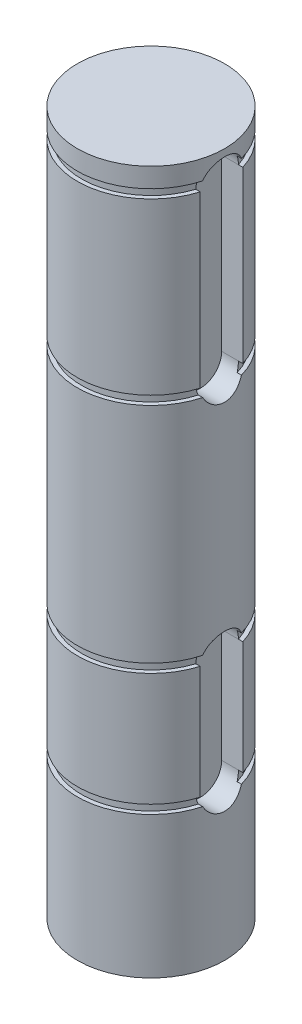
SolidWorks part; units mm, degrees
ref_plane "Front Plane" through (0, 0, 0) normal (0, 0, 1) x (1, 0, 0)
ref_plane "Top Plane" through (0, 0, 0) normal (0, 1, 0) x (1, 0, 0)
ref_plane "Right Plane" through (0, 0, 0) normal (1, 0, 0) x (0, 0, -1)
sketch "Sketch1" plane through (0, 0, 0) normal (0, 1, 0) x (1, 0, 0)
  circle A0 centre (0, 0) radius 8.255
extrude "Boss-Extrude1" add sketch "Sketch1" along normal blind 78.7908 contours A0
sketch "Sketch3" plane through (0, 0, 0) normal (1, 0, 0) x (0, 0, -1)
  line L0 (-8.255, 0) -> (8.255, 0) construction
  line L1 (-35.9296, 16.8656) -> (-7.7851, 16.8656)
  line L2 (-35.9296, 16.8656) -> (-35.9296, 15.875)
  line L3 (-35.9296, 15.875) -> (-7.7851, 15.875)
  line L4 (-7.7851, 16.8656) -> (-7.7851, 15.875)
  line L5 (-8.255, 78.7908) -> (-8.255, 0) construction
  line L6 (0, 29.9273) -> (0, 6.5085) construction
  dimension "D1" = 28.1445
  dimension "D2" = 15.875
  dimension "D3" = 0.9906
  dimension "D4" = 0.4699
revolve "Cut-Revolve1" cut sketch "Sketch3" angle 360 about L6
sketch "Sketch4" plane through (0, 0, 0) normal (1, 0, 0) x (0, 0, -1)
  line L0 (-7.7851, 16.8656) -> (7.7851, 16.8656) construction
  line L1 (-20.6586, 30.5562) -> (-7.7851, 30.5562)
  line L2 (-20.6586, 30.5562) -> (-20.6586, 29.5656)
  line L3 (-20.6586, 29.5656) -> (-7.7851, 29.5656)
  line L4 (-7.7851, 30.5562) -> (-7.7851, 29.5656)
  line L5 (-8.255, 78.7908) -> (-8.255, 16.8656) construction
  line L6 (0, 33.7907) -> (0, 24.3351) construction
  dimension "D1" = 12.7
  dimension "D2" = 0.9906
  dimension "D3" = 0.4699
revolve "Cut-Revolve2" cut sketch "Sketch4" angle 360 about L6
sketch "Sketch5" plane through (0, 0, 0) normal (1, 0, 0) x (0, 0, -1)
  line L0 (-7.7851, 30.5562) -> (7.7851, 30.5562) construction
  line L1 (-26.2954, 56.5658) -> (-7.7851, 56.5658)
  line L2 (-26.2954, 56.5658) -> (-26.2954, 55.5752)
  line L3 (-26.2954, 55.5752) -> (-7.7851, 55.5752)
  line L4 (-7.7851, 56.5658) -> (-7.7851, 55.5752)
  line L5 (-8.255, 78.7908) -> (-8.255, 30.5562) construction
  line L6 (0, 60.6078) -> (0, 49.3632) construction
  dimension "D1" = 25.019
  dimension "D2" = 0.9906
  dimension "D3" = 0.4699
revolve "Cut-Revolve3" cut sketch "Sketch5" angle 360 about L6
sketch "Sketch6" plane through (0, 0, 0) normal (1, 0, 0) x (0, 0, -1)
  line L0 (-7.7851, 56.5658) -> (7.7851, 56.5658) construction
  line L1 (-21.1239, 76.6064) -> (-7.7851, 76.6064)
  line L2 (-21.1239, 76.6064) -> (-21.1239, 75.6158)
  line L3 (-21.1239, 75.6158) -> (-7.7851, 75.6158)
  line L4 (-7.7851, 76.6064) -> (-7.7851, 75.6158)
  line L5 (-8.255, 78.7908) -> (-8.255, 56.5658) construction
  line L6 (0, 77.1554) -> (0, 69.2288) construction
  dimension "D1" = 19.05
  dimension "D2" = 0.9906
  dimension "D3" = 0.4699
revolve "Cut-Revolve4" cut sketch "Sketch6" angle 360 about L6
ref_plane "Plane1" through (8.2804, 0, 0) normal (1, 0, 0) x (0, 0, -1)
sketch "Sketch7" plane through (8.2804, 0, 0) normal (1, 0, 0) x (0, 0, -1)
  line L0 (0, 75.6158) -> (0, 56.5658) construction
  line L1 (8.255, 75.6158) -> (-8.255, 75.6158) construction
  line L2 (-7.7851, 56.5658) -> (7.7851, 56.5658) construction
  line L3 (2.3876, 75.6158) -> (2.3876, 56.5658)
  line L4 (-2.3876, 75.6158) -> (-2.3876, 56.5658)
  arc A0 (2.3876, 75.6158) -> (-2.3876, 75.6158) centre (0, 75.6158) ccw
  arc A1 (-2.3876, 56.5658) -> (2.3876, 56.5658) centre (0, 56.5658) ccw
  point P6 (0, 66.0908)
extrude "Cut-Extrude2" cut sketch "Sketch7" against normal blind 2.7432 contours L4 A1 L3 A0
sketch "Sketch8" plane through (8.2804, 0, 0) normal (1, 0, 0) x (0, 0, -1)
  line L0 (0, 29.5656) -> (0, 16.8656) construction
  line L1 (8.255, 29.5656) -> (-8.255, 29.5656) construction
  line L2 (-7.7851, 16.8656) -> (7.7851, 16.8656) construction
  line L3 (2.3876, 29.5656) -> (2.3876, 16.8656)
  line L4 (-2.3876, 29.5656) -> (-2.3876, 16.8656)
  arc A0 (2.3876, 29.5656) -> (-2.3876, 29.5656) centre (0, 29.5656) ccw
  arc A1 (-2.3876, 16.8656) -> (2.3876, 16.8656) centre (0, 16.8656) ccw
  point P6 (0, 23.2156)
extrude "Cut-Extrude3" cut sketch "Sketch8" against normal blind 2.7432
